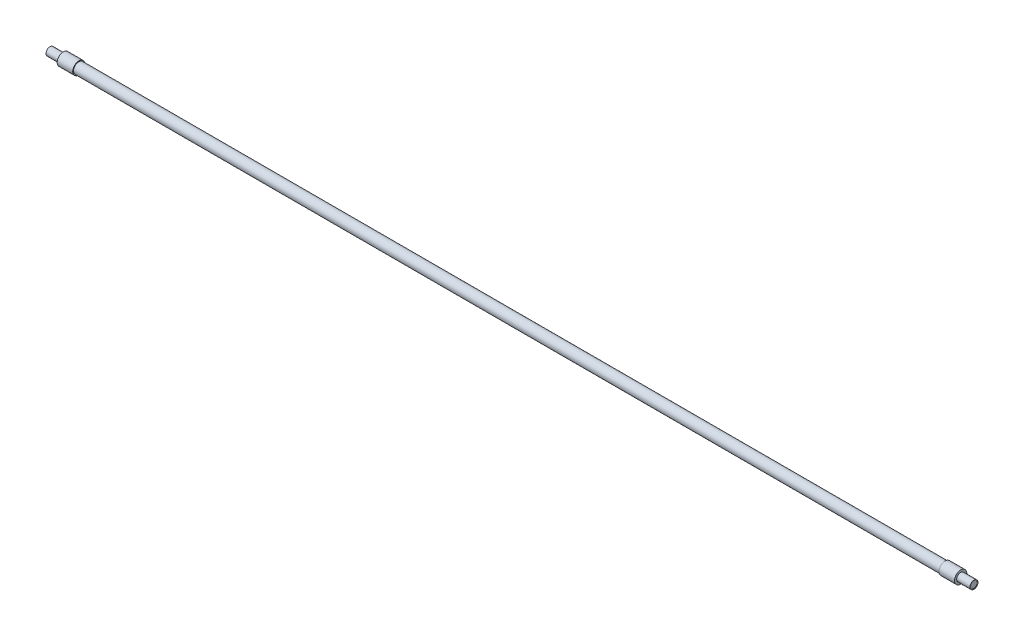
SolidWorks part; units mm, degrees
ref_plane "Front Plane" through (0, 0, 0) normal (0, 0, 1) x (1, 0, 0)
ref_plane "Top Plane" through (0, 0, 0) normal (0, 1, 0) x (1, 0, 0)
ref_plane "Right Plane" through (0, 0, 0) normal (1, 0, 0) x (0, 0, -1)
sketch "Sketch3" plane through (0, 0, 0) normal (0, 0, 1) x (1, 0, 0)
  line L0 (0, 0) -> (34.4478, 0) construction
  line L1 (0, 0) -> (0, 3.95)
  line L2 (0, 3.95) -> (13.1, 3.95)
  line L3 (13.1, 3.95) -> (13.1, 6.05)
  line L4 (13.1, 6.05) -> (28.4, 6.05)
  line L5 (28.4, 6.05) -> (28.4, 0)
  line L6 (28.4, 0) -> (0, 0)
  dimension "D1" = 28.4
  dimension "D2" = 13.1
  dimension "D3" = 6.05
  dimension "D4" = 3.95
revolve "Revolve1" add sketch "Sketch3" angle 360 about L0
fillet "Fillet1" radius 0.4 1 edges at (13.1, 0, 3.95)
sketch "Sketch6" plane through (28.4, 0, 0) normal (1, 0, 0) x (0, 0, -1)
  circle A0 centre (0, 0) radius 5.25
  dimension "D1" = 10.5
extrude "Boss-Extrude1" add sketch "Sketch6" along normal blind 853.2
ref_plane "Plane1" through (455, 0, 0) normal (1, 0, 0) x (0, 0, -1)
mirror "Mirror1" about plane through (455, 0, 0) normal (1, 0, 0) of "Revolve1"
sketch "Sketch7" plane through (910, 0, 0) normal (1, 0, 0) x (0, 0, -1)
  circle A0 centre (0, 0) radius 3.175
  dimension "D1" = 6.35
extrude "Cut-Extrude1" cut sketch "Sketch7" against normal blind 0.2
sketch "Sketch9" plane through (0, 0, 0) normal (-1, 0, 0) x (0, 0, 1)
  circle A0 centre (0, 0) radius 3.175
extrude "Cut-Extrude2" cut sketch "Sketch9" against normal blind 0.2
